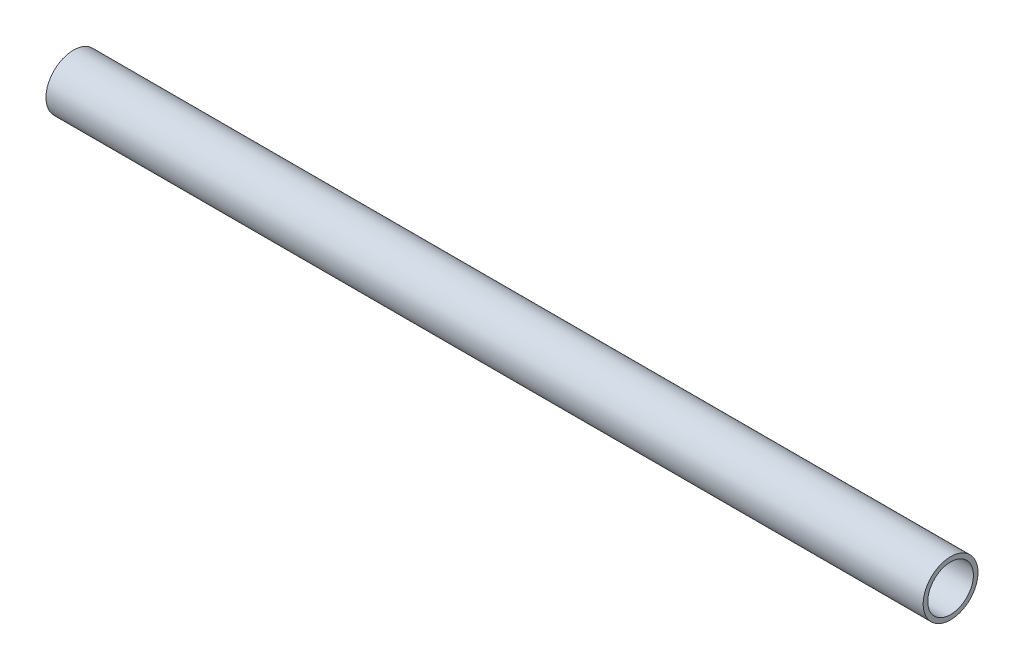
SolidWorks part; units mm, degrees
ref_plane "Front Plane" through (0, 0, 0) normal (0, 0, 1) x (1, 0, 0)
ref_plane "Top Plane" through (0, 0, 0) normal (0, 1, 0) x (1, 0, 0)
ref_plane "Right Plane" through (0, 0, 0) normal (1, 0, 0) x (0, 0, -1)
sketch "Sketch1" plane through (0, 0, 0) normal (0, 0, 1) x (1, 0, 0)
  line L0 (17.6222, 1527.5128) -> (220.8257, 1527.5128)
other "Pipe 0.5 SCH 40(1)"
ref_plane "Plane1" through (17.6222, 1527.5128, 0) normal (1, 0, 0) x (0, 1, 0)
sketch "Sketch11" plane through (17.6222, 1527.5128, 0) normal (1, 0, 0) x (0, 1, 0)
  circle A0 centre (0, 0) radius 5.2832
  circle A1 centre (0, 0) radius 6.35
  point P5 (0, 0)
  dimension "D1" = 12.7
  dimension "D2" = 10.5664
